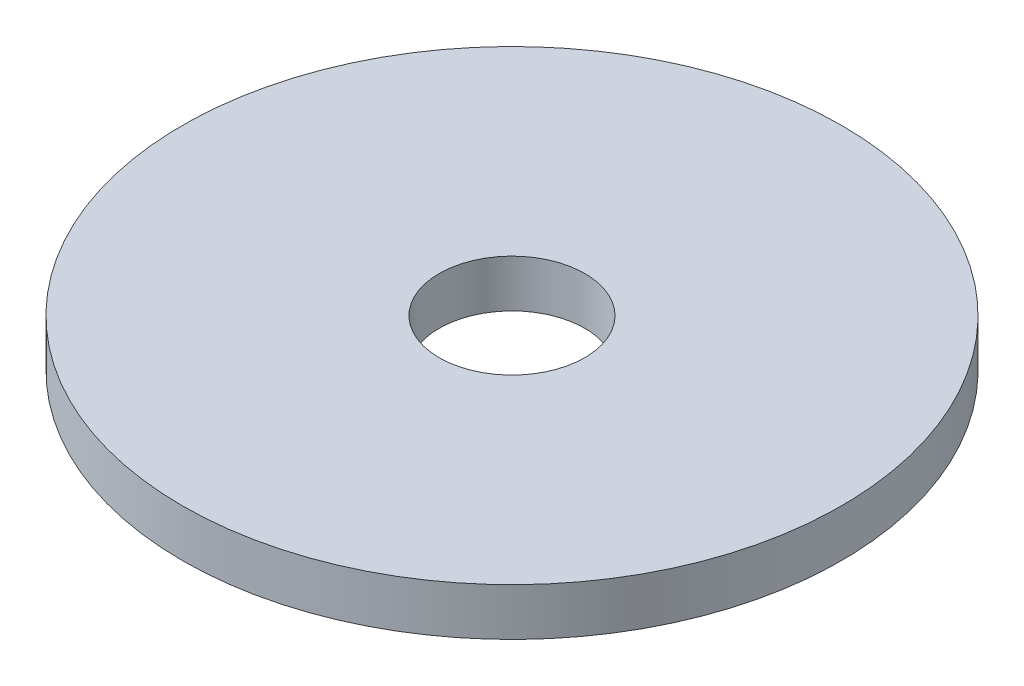
SolidWorks part; units mm, degrees
material "Alloy Steel"
ref_plane "Plane1" through (0, 0, 0) normal (0, 0, 1) x (1, 0, 0)
ref_plane "Plane2" through (0, 0, 0) normal (0, 1, 0) x (1, 0, 0)
ref_plane "Plane3" through (0, 0, 0) normal (1, 0, 0) x (0, 0, -1)
sketch "Sketch2" plane through (0, 0, 0) normal (0, 1, 0) x (1, 0, 0)
  circle A0 centre (0, 0) radius 11.1125
  circle A1 centre (0, 0) radius 2.4574
  dimension "ID" = 4.9149
  dimension "OD" = 22.225
extrude "Base-Extrude" add sketch "Sketch2" along normal blind 1.6002
